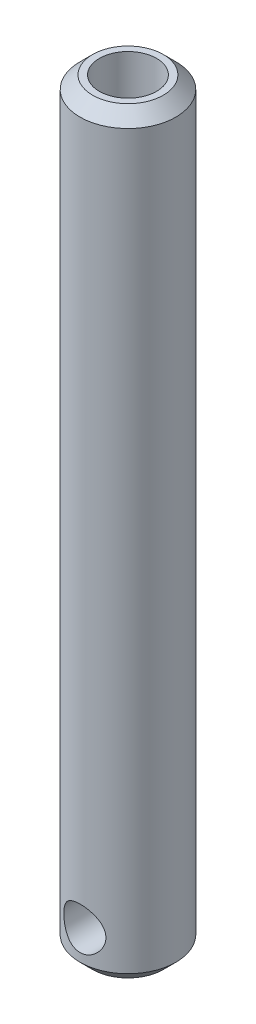
SolidWorks part; units mm, degrees
ref_plane "Front Plane" through (0, 0, 0) normal (0, 0, 1) x (1, 0, 0)
ref_plane "Top Plane" through (0, 0, 0) normal (0, 1, 0) x (1, 0, 0)
ref_plane "Right Plane" through (0, 0, 0) normal (1, 0, 0) x (0, 0, -1)
sketch "Sketch1" plane through (0, 0, 0) normal (0, 1, 0) x (1, 0, 0)
  circle A0 centre (0, 0) radius 5.7
  dimension "D1" = 11.4
extrude "Boss-Extrude1" add sketch "Sketch1" along normal blind 90
hole_wizard "M8 Tapped Hole1" positions "Sketch2" profile "Sketch3" tap size "M8" standard "ISO"
sketch "Sketch2" plane through (0, 90, 0) normal (0, 1, 0) x (1, 0, 0)
  point P0 (0, 0)
sketch "Sketch3" plane through (0, 90, 0) normal (1, 0, 0) x (0, 0, 1)
  line L0 (0, 0) -> (0, 36.963)
  line L1 (0, 36.963) -> (3.4, 35)
  line L2 (3.4, 35) -> (3.4, 0)
  line L5 (3.4, 0) -> (0, 0)
  line L10 (0, 36.963) -> (-3.4, 35) construction
  line L11 (0, -6.35) -> (0, 107.95) construction
  dimension "Tap Drill Dia." = 6.8
  dimension "Tap Drill Depth" = 35
  dimension "Drill Angle" = 120
cosmetic thread "Hole Thread1"
chamfer "Chamfer2" distance 1.5 angle 45 2 edges at (0, 0, 5.7) (0, 90, 5.7)
sketch "Sketch4" plane through (0, 0, 0) normal (0, 0, 1) x (1, 0, 0)
  circle A0 centre (0, 5) radius 2.5
  point P2 (0, 0)
  dimension "D1" = 5
  dimension "D2" = 5
extrude "Cut-Extrude1" cut sketch "Sketch4" against normal mid plane 20
